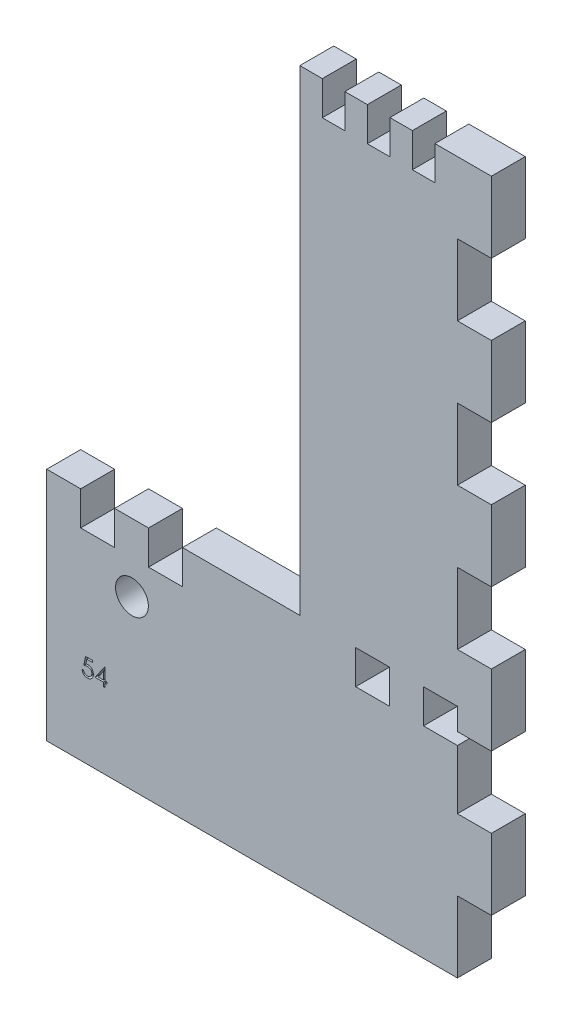
SolidWorks part; units mm, degrees
material "Acrylic (Medium-high impact)"
ref_plane "Front Plane" through (0, 0, 0) normal (0, 0, 1) x (1, 0, 0)
ref_plane "Top Plane" through (0, 0, 0) normal (0, 1, 0) x (1, 0, 0)
ref_plane "Right Plane" through (0, 0, 0) normal (1, 0, 0) x (0, 0, -1)
sketch "Sketch6" plane through (0, 0, 0) normal (0, 0, 1) x (1, 0, 0)
  line L5 (107.544, 124.6539) -> (188.794, 124.6539)
  line L6 (107.544, 124.6539) -> (107.544, -5.3461)
  line L7 (107.544, -5.3461) -> (188.794, -5.3461)
  line L8 (188.794, 124.6539) -> (188.794, -5.3461)
  line L9 (107.544, 124.6539) -> (153.794, 124.6539)
  line L10 (107.544, 124.6539) -> (107.544, 37.6539)
  line L11 (107.544, 37.6539) -> (153.794, 37.6539)
  line L12 (153.794, 124.6539) -> (153.794, 37.6539)
  line L13 (113.744, 37.6539) -> (119.944, 37.6539)
  line L14 (113.744, 37.6539) -> (113.744, 31.4539)
  line L15 (113.744, 31.4539) -> (119.944, 31.4539)
  line L16 (119.944, 37.6539) -> (119.944, 31.4539)
  line L18 (126.144, 37.6539) -> (132.344, 37.6539)
  line L19 (126.144, 37.6539) -> (126.144, 31.4539)
  line L20 (126.144, 31.4539) -> (132.344, 31.4539)
  line L21 (132.344, 37.6539) -> (132.344, 31.4539)
  line L26 (188.794, 111.6539) -> (182.594, 111.6539)
  line L27 (188.794, 111.6539) -> (188.794, 98.6539)
  line L28 (188.794, 98.6539) -> (182.594, 98.6539)
  line L29 (182.594, 111.6539) -> (182.594, 98.6539)
  line L30 (188.794, 85.6539) -> (182.594, 85.6539)
  line L31 (188.794, 85.6539) -> (188.794, 72.6539)
  line L32 (188.794, 72.6539) -> (182.594, 72.6539)
  line L33 (182.594, 85.6539) -> (182.594, 72.6539)
  line L34 (188.794, 59.6539) -> (182.594, 59.6539)
  line L35 (188.794, 59.6539) -> (188.794, 46.6539)
  line L36 (188.794, 46.6539) -> (182.594, 46.6539)
  line L37 (182.594, 59.6539) -> (182.594, 46.6539)
  line L42 (188.794, 33.6539) -> (182.594, 33.6539)
  line L43 (188.794, 33.6539) -> (188.794, 20.6539)
  line L44 (188.794, 20.6539) -> (182.594, 20.6539)
  line L45 (182.594, 33.6539) -> (182.594, 20.6539)
  line L46 (188.794, 7.6539) -> (182.594, 7.6539)
  line L47 (188.794, 7.6539) -> (188.794, -5.3461)
  line L48 (188.794, -5.3461) -> (182.594, -5.3461)
  line L49 (182.594, 7.6539) -> (182.594, -5.3461)
  line L50 (157.908, 124.6539) -> (162.022, 124.6539)
  line L51 (157.908, 124.6539) -> (157.908, 118.4539)
  line L52 (157.908, 118.4539) -> (162.022, 118.4539)
  line L53 (162.022, 124.6539) -> (162.022, 118.4539)
  line L54 (166.136, 124.6539) -> (170.25, 124.6539)
  line L55 (166.136, 124.6539) -> (166.136, 118.4539)
  line L56 (166.136, 118.4539) -> (170.25, 118.4539)
  line L57 (170.25, 124.6539) -> (170.25, 118.4539)
  line L58 (174.364, 124.6539) -> (178.478, 124.6539)
  line L59 (174.364, 124.6539) -> (174.364, 118.4539)
  line L60 (174.364, 118.4539) -> (178.478, 118.4539)
  line L61 (178.478, 124.6539) -> (178.478, 118.4539)
  line L62 (182.594, 37.6539) -> (176.394, 37.6539)
  line L63 (182.594, 37.6539) -> (182.594, 31.4539)
  line L64 (182.594, 31.4539) -> (176.394, 31.4539)
  line L65 (176.394, 37.6539) -> (176.394, 31.4539)
  line L66 (170.194, 37.6539) -> (163.994, 37.6539)
  line L67 (170.194, 37.6539) -> (170.194, 31.4539)
  line L68 (170.194, 31.4539) -> (163.994, 31.4539)
  line L69 (163.994, 37.6539) -> (163.994, 31.4539)
  circle A2 centre (123.1151, 25.2595) radius 3
  point P56 (123.1151, 25.2595)
  dimension "D1" = 81.25
  dimension "D2" = 130
  dimension "D3" = 87
  dimension "D4" = 46.25
  dimension "D5" = 6.2
  dimension "D6" = 6.2
  dimension "D7" = 6.2
  dimension "D8" = 6.2
  dimension "D9" = 6.2
  dimension "D10" = 6.2
  dimension "D11" = 13
  dimension "D12" = 6.2
  dimension "D13" = 13
  dimension "D14" = 13
  dimension "D15" = 6.2
  dimension "D16" = 13
  dimension "D17" = 13
  dimension "D18" = 6.2
  dimension "D19" = 13
  dimension "D20" = 6.2
  dimension "D21" = 13
  dimension "D22" = 13
  dimension "D23" = 13
  dimension "D24" = 6.2
  dimension "D25" = 4.114
  dimension "D26" = 4.114
  dimension "D27" = 4.114
  dimension "D28" = 6.2
  dimension "D29" = 6.2
  dimension "D30" = 4.114
  dimension "D31" = 4.114
  dimension "D32" = 6.2
  dimension "D33" = 4.114
  dimension "D34" = 6.2
  dimension "D35" = 6.2
  dimension "D36" = 6.2
  dimension "D37" = 6.2
  dimension "D38" = 6.2
extrude "Boss-Extrude4" add sketch "Sketch6" along normal blind 6.2 contours L65 L62 L63 L42 L8 L36 L37 L34 L32 L33 L30 L28 L29 L26 L5 L61 L60 L59 L57 L56 L55 L53 L52 L51 L12 L11 L21 L20 L19 L16 L15 L14 L6 L7 L49 L46 L44 L45 L64 L69 L66
sketch "Sketch7" plane through (0, 0, 6.2) normal (0, 0, 1) x (1, 0, 0)
  text T0 "54\r\n"
extrude "Cut-Extrude3" cut sketch "Sketch7" against normal blind 1
